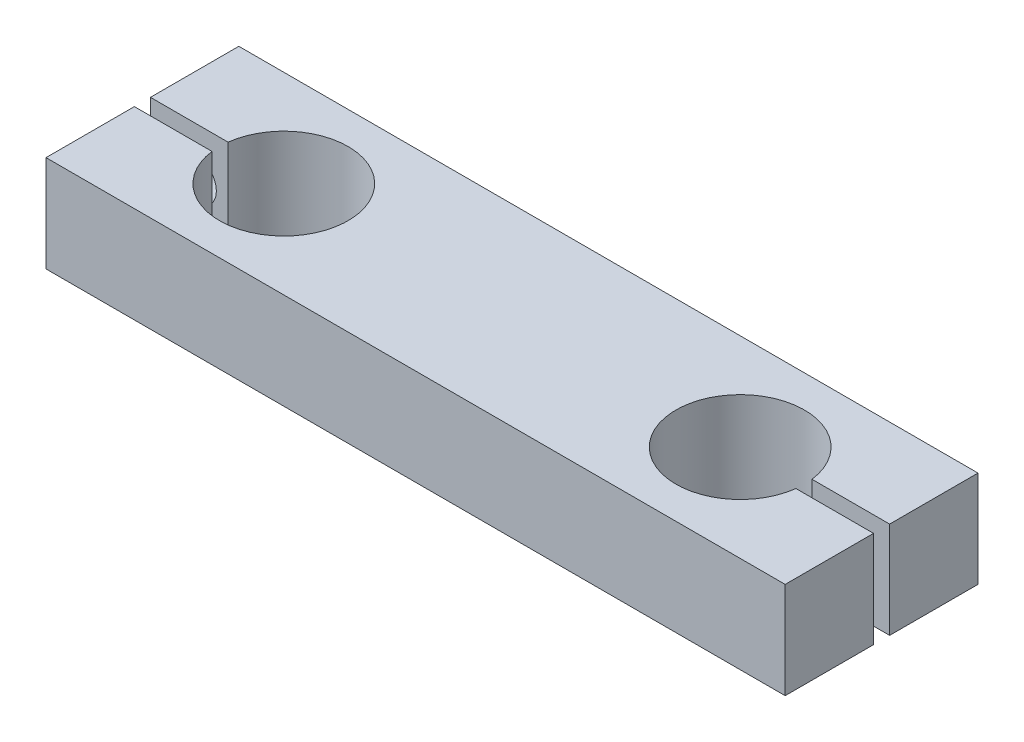
SolidWorks part; units mm, degrees
material "1060 Alloy"
ref_plane "Front Plane" through (0, 0, 0) normal (0, 0, 1) x (1, 0, 0)
ref_plane "Top Plane" through (0, 0, 0) normal (0, 1, 0) x (1, 0, 0)
ref_plane "Right Plane" through (0, 0, 0) normal (1, 0, 0) x (0, 0, -1)
sketch "Sketch1" plane through (0, 0, 0) normal (0, 1, 0) x (1, 0, 0)
  line L0 (0, 0) -> (87.1676, 0) construction
  line L1 (-57.5, 15) -> (57.5, 15)
  line L2 (-57.5, 15) -> (-57.5, -15)
  line L3 (-57.5, -15) -> (57.5, -15)
  line L4 (57.5, 15) -> (57.5, -15)
  line L5 (-57.5, 15) -> (57.5, -15) construction
  line L6 (-57.5, -15) -> (57.5, 15) construction
  line L7 (87.1676, 0) -> (0, 0) construction
  line L8 (0, 0) -> (-109.1888, 0) construction
  line L9 (-45.4216, 1.25) -> (-57.5, 1.25)
  line L10 (-57.5, 1.25) -> (-57.5, -1.25)
  line L11 (-57.5, -1.25) -> (-45.4216, -1.25)
  line L12 (45.4216, 1.25) -> (57.5, 1.25)
  line L13 (57.5, 1.25) -> (57.5, -1.25)
  line L14 (57.5, -1.25) -> (45.4216, -1.25)
  circle A0 centre (-35.5, 0) radius 10
  circle A1 centre (35.5, 0) radius 10
  point P0 (0, 0)
  dimension "D3" = 20
  dimension "D4" = 20
  dimension "D1" = 115
  dimension "D2" = 30
  dimension "D5" = 15
  dimension "D6" = 2.5
  dimension "D7" = 1.25
  dimension "D8" = 22
  dimension "D9" = 71
  dimension "D10" = 22
  dimension "D11" = 2.5
  dimension "D12" = 1.25
extrude "Boss-Extrude1" add sketch "Sketch1" along normal blind 15 contours A1 L12 L4 L1 L2 L9 A0 L11 L3 L14
sketch "Sketch2" plane through (0, 0, -15) normal (0, 0, -1) x (-1, 0, 0)
  line L0 (-57.5, 15) -> (-57.5, 0) construction
  line L1 (57.5, 15) -> (-57.5, 15) construction
  line L2 (57.5, 15) -> (57.5, 0) construction
  circle A0 centre (-50.5, 7.5) radius 5.25
  circle A1 centre (50.5, 7.5) radius 5.25
  dimension "D1" = 10.5
  dimension "D2" = 10.5
  dimension "D3" = 7
  dimension "D4" = 7.5
  dimension "D5" = 7.5
  dimension "D6" = 7
extrude "Cut-Extrude1" cut sketch "Sketch2" against normal blind 7
sketch "Sketch3" plane through (0, 0, -8) normal (0, 0, -1) x (-1, 0, 0)
  circle A0 centre (-50.5, 7.5) radius 3.25
  circle A1 centre (50.5, 7.5) radius 3.25
  dimension "D1" = 6.5
  dimension "D2" = 6.5
extrude "Cut-Extrude2" cut sketch "Sketch3" against normal blind 20
